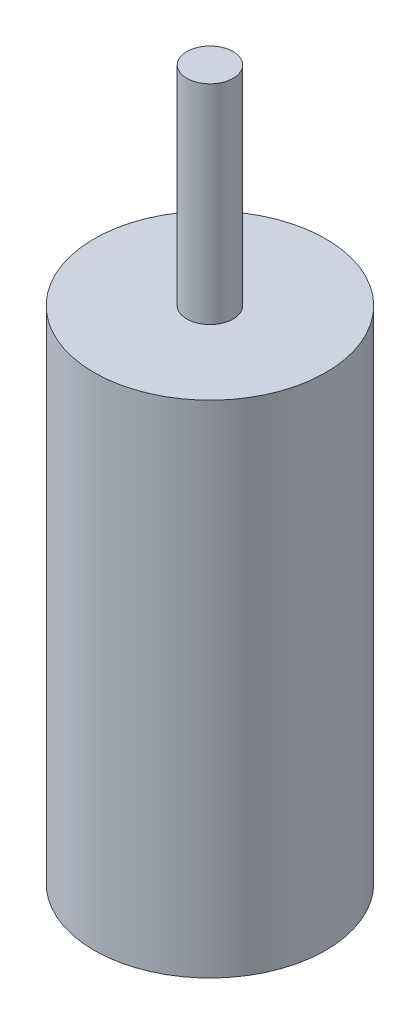
SolidWorks part; units mm, degrees
ref_plane "Front Plane" through (0, 0, 0) normal (0, 0, 1) x (1, 0, 0)
ref_plane "Top Plane" through (0, 0, 0) normal (0, 1, 0) x (1, 0, 0)
ref_plane "Right Plane" through (0, 0, 0) normal (1, 0, 0) x (0, 0, -1)
sketch "Sketch1" plane through (0, 0, 0) normal (0, 1, 0) x (1, 0, 0)
  circle A0 centre (0, 0) radius 10
  dimension "D1" = 20
extrude "Boss-Extrude1" add sketch "Sketch1" along normal blind 43.2
sketch "Sketch2" plane through (0, 43.2, 0) normal (0, 1, 0) x (1, 0, 0)
  circle A0 centre (0, 0) radius 2
  dimension "D1" = 4
extrude "Boss-Extrude2" add sketch "Sketch2" along normal blind 18
